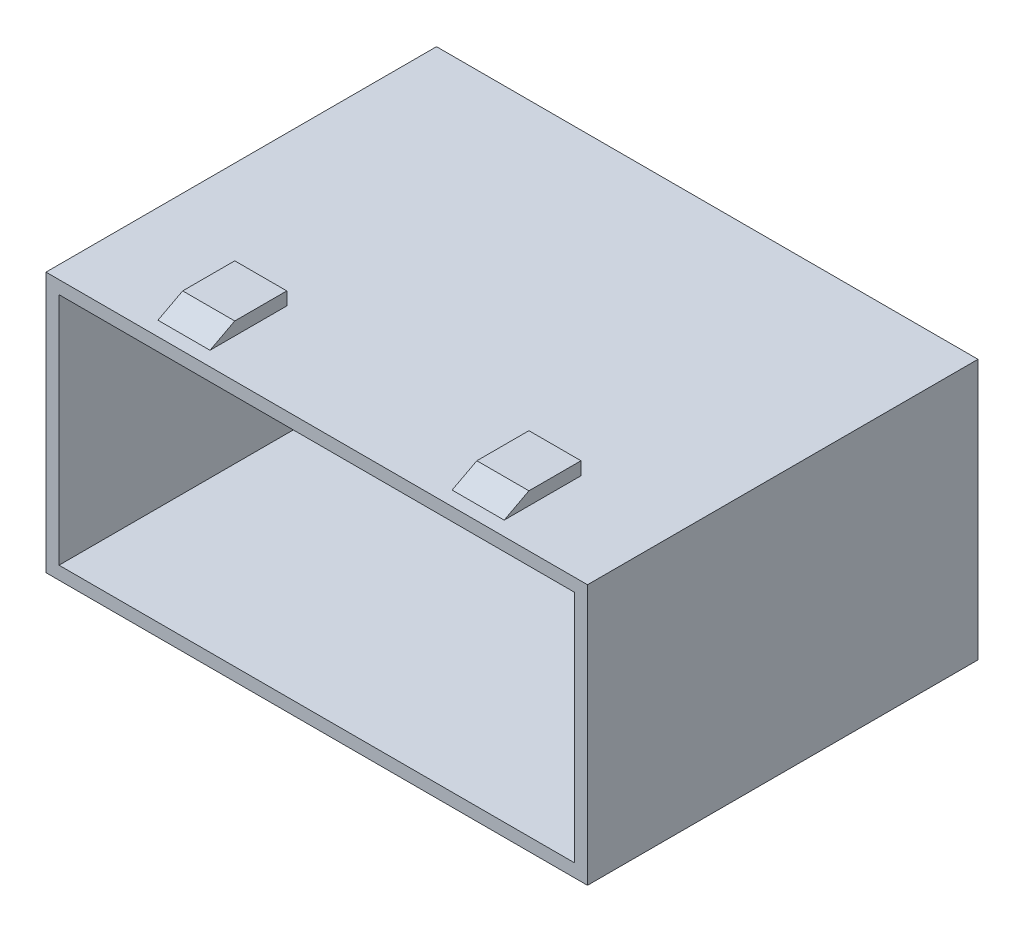
SolidWorks part; units mm, degrees
ref_plane "Front Plane" through (0, 0, 0) normal (0, 0, 1) x (1, 0, 0)
ref_plane "Top Plane" through (0, 0, 0) normal (0, 1, 0) x (1, 0, 0)
ref_plane "Right Plane" through (0, 0, 0) normal (1, 0, 0) x (0, 0, -1)
sketch "Sketch1" plane through (0, 0, 0) normal (0, 0, 1) x (1, 0, 0)
  line L0 (19.8, 9) -> (19.8, -9)
  line L1 (-20.8, 10) -> (20.8, 10)
  line L2 (-20.8, 10) -> (-20.8, -10)
  line L3 (-20.8, -10) -> (20.8, -10)
  line L4 (20.8, 10) -> (20.8, -10)
  line L5 (-20.8, 10) -> (20.8, -10) construction
  line L6 (-20.8, -10) -> (20.8, 10) construction
  line L7 (-19.8, -9) -> (19.8, -9)
  line L8 (-19.8, 9) -> (-19.8, -9)
  line L9 (-19.8, 9) -> (19.8, 9)
  point P0 (0, 0)
  dimension "D1" = 1
extrude "Boss-Extrude2" add sketch "Sketch1" along normal blind 10
sketch "Sketch2" plane through (0, -10, 0) normal (0, -1, 0) x (1, 0, 0)
  line L0 (0, 10) -> (0, 0)
  line L1 (-20.8, 10) -> (20.8, 10) construction
  line L3 (-9.3, 10) -> (9.3, 10)
  line L4 (-9.3, 10) -> (-9.3, 0)
  line L5 (-9.3, 0) -> (9.3, 0)
  line L6 (9.3, 10) -> (9.3, 0)
  line L7 (-9.3, 10) -> (9.3, 0) construction
  line L8 (-9.3, 0) -> (9.3, 10) construction
  line L9 (9.3, 10) -> (13.3, 10)
  line L10 (9.3, 10) -> (9.3, 0)
  line L11 (9.3, 0) -> (13.3, 0)
  line L12 (13.3, 10) -> (13.3, 0)
  line L13 (-9.3, 10) -> (-13.3, 10)
  line L14 (-9.3, 10) -> (-9.3, 0)
  line L15 (-9.3, 0) -> (-13.3, 0)
  line L16 (-13.3, 10) -> (-13.3, 0)
  point P5 (0, 5)
  line M1 (-20.8, 0) -> (20.8, 0)
  line M3 (20.8, 10) -> (-20.8, 10)
extrude "Boss-Extrude3" add sketch "Sketch2" along normal blind 1 contours L16 L4 M3 M1 | L12 L6 M3 M1
sketch "Sketch3" plane through (-13.3, 0, 0) normal (-1, 0, 0) x (0, 0, 1)
  line L0 (7, -11) -> (8.9001, -10)
  line L1 (10, -11) -> (7, -11)
  line L2 (10, -11) -> (10, -10)
  line L3 (10, -10) -> (7, -10)
  line L4 (7, -11) -> (7, -10)
  line L5 (0, -11) -> (0, -10) construction
  line L6 (7, -10) -> (3, -10)
  line L7 (7, -10) -> (7, -11)
  line L8 (7, -11) -> (3, -11)
  line L9 (3, -10) -> (3, -11)
  line L10 (3, -10) -> (0, -10)
  line L11 (3, -10) -> (3, -11)
  line L12 (3, -11) -> (0, -11)
  line L13 (0, -10) -> (0, -11)
  line L14 (10, -11) -> (0, -11) construction
  line M1 (10, -10) -> (0, -10)
  line M2 (0, -10) -> (0, -11)
  line M3 (0, -11) -> (10, -11)
  line M4 (10, -11) -> (10, -10)
extrude "Cut-Extrude1" cut sketch "Sketch3" against normal blind 27 contours L0 M3 M4 M1 | L9 M1 M2 M3
sketch "Sketch4" plane through (0, 10, 0) normal (0, 1, 0) x (1, 0, 0)
  line L0 (0, -10) -> (0, 0)
  line L1 (20.8, -10) -> (-20.8, -10) construction
  line L2 (20.8, 0) -> (-20.8, 0) construction
  line L4 (9.3, -10) -> (-9.3, -10)
  line L5 (9.3, -10) -> (9.3, 0)
  line L6 (9.3, 0) -> (-9.3, 0)
  line L7 (-9.3, -10) -> (-9.3, 0)
  line L8 (9.3, -10) -> (-9.3, 0) construction
  line L9 (9.3, 0) -> (-9.3, -10) construction
  line L10 (-9.3, -10) -> (-13.3, -10)
  line L11 (-9.3, -10) -> (-9.3, 0)
  line L12 (-9.3, 0) -> (-13.3, 0)
  line L13 (-13.3, -10) -> (-13.3, 0)
  line L14 (9.3, -10) -> (13.3, -10)
  line L15 (9.3, -10) -> (9.3, 0)
  line L16 (9.3, 0) -> (13.3, 0)
  line L17 (13.3, -10) -> (13.3, 0)
  point P6 (0, -5)
  line M1 (20.8, 0) -> (-20.8, 0)
  line M3 (-20.8, -10) -> (20.8, -10)
extrude "Boss-Extrude4" add sketch "Sketch4" along normal blind 1 contours L17 L5 M3 M1 | L13 L7 M3 M1
sketch "Sketch5" plane through (13.3, 0, 0) normal (1, 0, 0) x (0, 0, -1)
  line L1 (-10, 11) -> (0, 11) construction
  line L2 (-10, 10) -> (0, 10) construction
  line L3 (-10, 11) -> (-7, 11)
  line L4 (-10, 11) -> (-10, 10)
  line L5 (-10, 10) -> (-7, 10)
  line L6 (-7, 11) -> (-7, 10)
  line L7 (-10, 10) -> (0, 10) construction
  line L8 (-7, 11) -> (-3, 11)
  line L9 (-7, 11) -> (-7, 10)
  line L10 (-7, 10) -> (-3, 10)
  line L11 (-3, 11) -> (-3, 10)
  line L12 (-7, 11) -> (-8.9001, 10)
  line M1 (-10, 10) -> (0, 10)
  line M2 (0, 10) -> (0, 11)
  line M3 (0, 11) -> (-10, 11)
  line M4 (-10, 11) -> (-10, 10)
extrude "Cut-Extrude2" cut sketch "Sketch5" against normal blind 27 contours L12 M3 M4 M1 | L11 M3 M1 M2
sketch "Sketch6" plane through (0, 0, 0) normal (0, 0, -1) x (-1, 0, 0)
  line L0 (19.8, -9) -> (-19.8, -9) construction
  line L1 (-20.8, 10) -> (20.8, 10)
  line L2 (-20.8, 10) -> (-20.8, -10)
  line L3 (-20.8, -10) -> (20.8, -10)
  line L4 (20.8, 10) -> (20.8, -10)
  line L5 (-20.8, 10) -> (20.8, -10) construction
  line L6 (-20.8, -10) -> (20.8, 10) construction
  line L7 (-19.8, 9) -> (19.8, 9)
  line L8 (-19.8, 9) -> (-19.8, -9)
  line L9 (-19.8, -9) -> (19.8, -9)
  line L10 (19.8, 9) -> (19.8, -9)
  line L11 (-19.8, 9) -> (19.8, -9) construction
  line L12 (-19.8, -9) -> (19.8, 9) construction
  point P0 (0, 0)
  point P7 (0, 0)
extrude "Boss-Extrude6" add sketch "Sketch6" along normal blind 19
sketch "Sketch7" plane through (0, 0, -19) normal (0, 0, -1) x (-1, 0, 0)
  line L1 (-20.8, 10) -> (20.8, 10)
  line L2 (-20.8, 10) -> (-20.8, -10)
  line L3 (-20.8, -10) -> (20.8, -10)
  line L4 (20.8, 10) -> (20.8, -10)
  line L5 (-20.8, 10) -> (20.8, -10) construction
  line L6 (-20.8, -10) -> (20.8, 10) construction
  point P0 (0, 0)
extrude "Boss-Extrude7" add sketch "Sketch7" along normal blind 1
